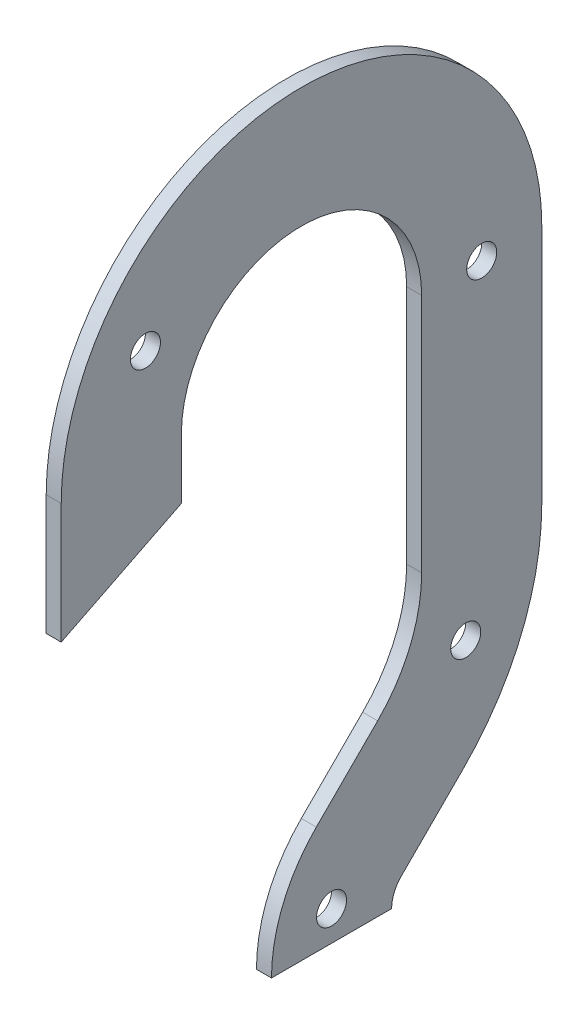
SolidWorks part; units mm, degrees
ref_plane "Front Plane" through (0, 0, 0) normal (0, 0, 1) x (1, 0, 0)
ref_plane "Top Plane" through (0, 0, 0) normal (0, 1, 0) x (1, 0, 0)
ref_plane "Right Plane" through (0, 0, 0) normal (1, 0, 0) x (0, 0, -1)
sketch "Sketch1" plane through (0, 0, 0) normal (1, 0, 0) x (0, 0, -1)
  line L0 (-50.8, 0) -> (-50.8, -25.4)
  line L2 (25.4, 0) -> (25.4, -50.8)
  line L4 (50.8, -50.8) -> (50.8, 0)
  line L5 (-6.35, 0) -> (-6.35, -103.13) construction
  line L6 (6.35, 0) -> (6.35, -103.13) construction
  line L7 (16.1006, -73.2506) -> (3.1306, -86.2206)
  line L8 (3.1306, -86.2206) -> (42.7043, -125.7943) construction
  line L9 (-25.4, 0) -> (-25.4, -12.7)
  line L10 (-50.8, -25.4) -> (-25.4, -12.7)
  line L11 (34.0612, -91.2112) -> (21.0911, -104.1812)
  line L12 (-6.35, -109.1089) -> (19.05, -109.1089)
  arc A0 (50.8, 0) -> (-50.8, 0) centre (0, 0) ccw
  arc A1 (25.4, 0) -> (-25.4, 0) centre (0, 0) ccw
  arc A2 (25.4, -50.8) -> (16.1006, -73.2506) centre (-6.35, -50.8) cw
  arc A3 (3.1306, -86.2206) -> (-6.35, -109.1089) centre (26.0189, -109.1089) ccw
  arc A4 (50.8, -50.8) -> (34.0612, -91.2112) centre (-6.35, -50.8) cw
  arc A5 (21.0911, -104.1812) -> (19.05, -109.1089) centre (26.0189, -109.1089) ccw
  dimension "D1" = 50.8
  dimension "D3" = 25.4
  dimension "D5" = 6.35
  dimension "D6" = 6.35
  dimension "D7" = 45
  dimension "D9" = 45
  dimension "D8" = 45
  dimension "D2" = 25.4
  dimension "D4" = 50.8
extrude "Boss-Extrude1" add sketch "Sketch1" along normal blind 3.175
sketch "Sketch2" plane through (3.175, 0, 0) normal (1, 0, 0) x (0, 0, -1)
  line L0 (25.4, 0) -> (25.4, -50.8) construction
  line L1 (22.9832, -62.9502) -> (55.7935, -76.5407) construction
  line L2 (-6.35, -109.1089) -> (19.05, -109.1089) construction
  circle A0 centre (38.1, 0) radius 3.175
  circle A1 centre (-32.9956, 19.05) radius 3.175
  arc A2 (38.1, 0) -> (-32.9956, 19.05) centre (0, 0) ccw construction
  circle A3 centre (34.7164, -67.8103) radius 3.175
  arc A4 (16.1006, -73.2506) -> (25.4, -50.8) centre (-6.35, -50.8) ccw construction
  circle A5 centre (6.35, -102.7589) radius 3.175
  dimension "D1" = 6.35
  dimension "D3" = 6.35
  dimension "D5" = 6.35
  dimension "D7" = 6.35
  dimension "D2" = 12.7
  dimension "D4" = 150
  dimension "D6" = 12.7
  dimension "D8" = 6.35
extrude "Cut-Extrude1" cut sketch "Sketch2" against normal through all
